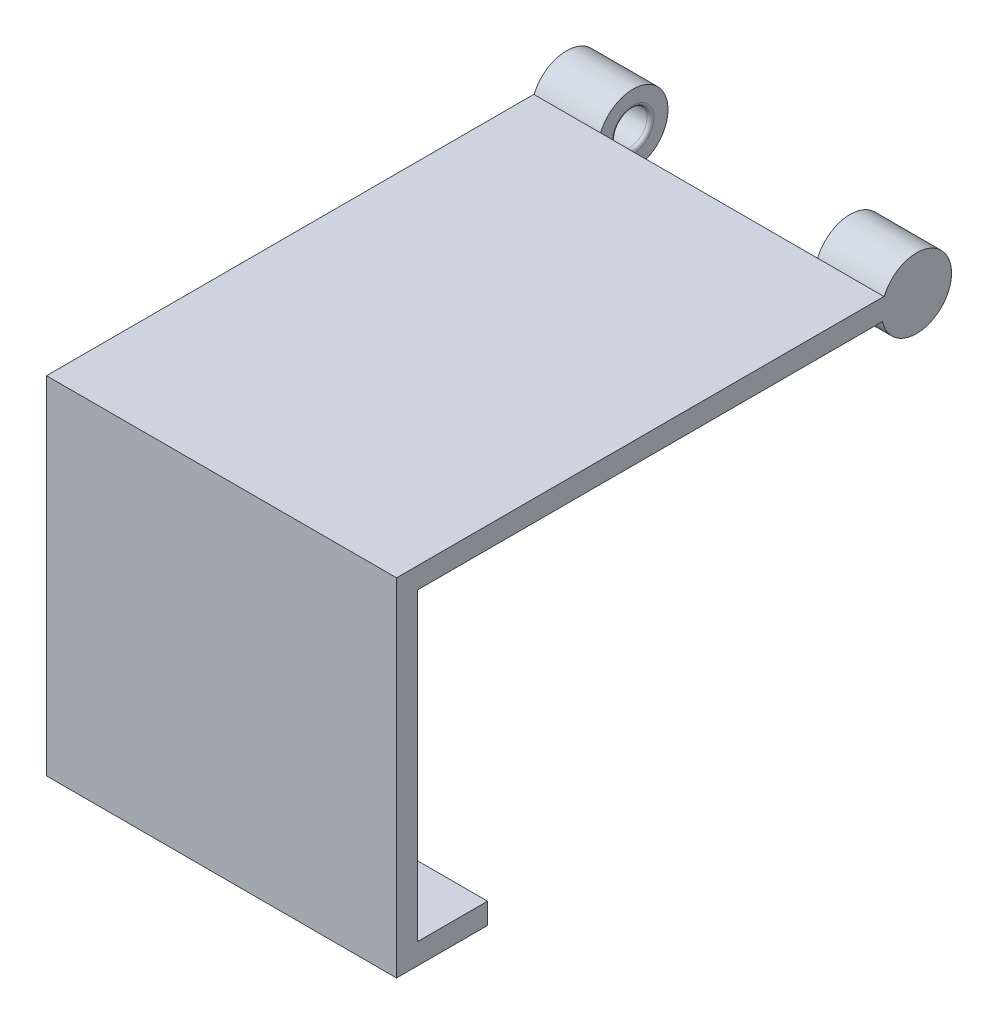
SolidWorks part; units mm, degrees
ref_plane "Front Plane" through (0, 0, 0) normal (0, 0, 1) x (1, 0, 0)
ref_plane "Top Plane" through (0, 0, 0) normal (0, 1, 0) x (1, 0, 0)
ref_plane "Right Plane" through (0, 0, 0) normal (1, 0, 0) x (0, 0, -1)
sketch "Sketch1" plane through (0, 0, 0) normal (1, 0, 0) x (0, 0, -1)
  line L0 (0, 0) -> (0, 43.5)
  line L1 (0, 43.5) -> (66.6, 43.5)
  line L2 (0, 0) -> (10, 0)
  line L3 (-3, -3) -> (10, -3)
  line L4 (-3, -3) -> (-3, 46.5)
  line L5 (-3, 46.5) -> (66.6, 46.5)
  line L6 (66.6, 46.5) -> (66.6, 43.5)
  line L7 (10, -3) -> (10, 0)
  dimension "D1" = 43.5
  dimension "D2" = 66.6
  dimension "D3" = 10
  dimension "D4" = 3
extrude "Boss-Extrude1" add sketch "Sketch1" along normal blind 50
sketch "Sketch2" plane through (50, 0, 0) normal (1, 0, 0) x (0, 0, -1)
  circle A0 centre (71.2725, 44.5651) radius 5
  dimension "D1" = 10
extrude "Boss-Extrude2" add sketch "Sketch2" against normal blind 9.5
ref_plane "Plane1" through (25, 0, 0) normal (1, 0, 0) x (0, 0, -1)
sketch "Sketch3" plane through (40.5, 0, 0) normal (-1, 0, 0) x (0, 0, 1)
  circle A0 centre (-71.2725, 44.5651) radius 2.5
  dimension "D1" = 5
extrude "Cut-Extrude1" cut sketch "Sketch3" against normal blind 4
fillet "Fillet1" radius 0.5 1 edges at (40.5, 44.5651, -68.7725)
mirror "Mirror2" about plane through (25, 0, 0) normal (1, 0, 0) of "Boss-Extrude2", "Cut-Extrude1", "Fillet1"
